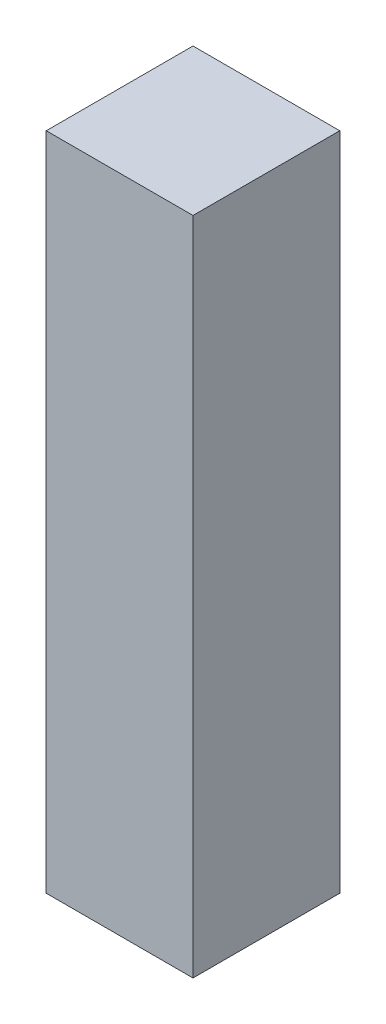
SolidWorks part; units mm, degrees
ref_plane "Front Plane" through (0, 0, 0) normal (0, 0, 1) x (1, 0, 0)
ref_plane "Top Plane" through (0, 0, 0) normal (0, 1, 0) x (1, 0, 0)
ref_plane "Right Plane" through (0, 0, 0) normal (1, 0, 0) x (0, 0, -1)
sketch "Sketch2" plane through (0, 0, 0) normal (0, 0, 1) x (1, 0, 0)
  line L1 (-1.5875, -7.1437) -> (1.5875, -7.1437)
  line L2 (-1.5875, -7.1437) -> (-1.5875, 7.1437)
  line L3 (-1.5875, 7.1437) -> (1.5875, 7.1437)
  line L4 (1.5875, -7.1437) -> (1.5875, 7.1437)
  line L5 (-1.5875, -7.1437) -> (1.5875, 7.1437) construction
  line L6 (-1.5875, 7.1437) -> (1.5875, -7.1437) construction
  point P0 (0, 0)
  dimension "D1" = 3.175
  dimension "D2" = 14.2875
extrude "Boss-Extrude1" add sketch "Sketch2" along normal blind 3.175
equation "\"side thickness\"= 1 / 8in"
equation "\"extrude thickness\"= 1 / 8in"
equation "\"length\"= 0.5625in"
equation "\"D1@Sketch2\"=\"side thickness\""
equation "\"D2@Sketch2\"=\"length\""
equation "\"D1@Boss-Extrude1\"=\"extrude thickness\""
